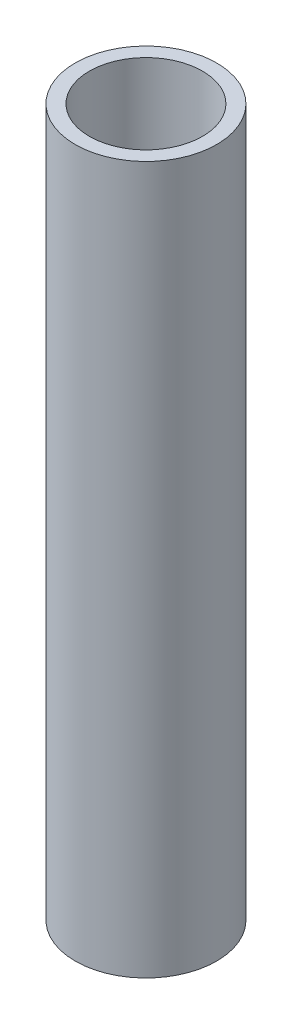
SolidWorks part; units mm, degrees
ref_plane "Front Plane" through (0, 0, 0) normal (0, 0, 1) x (1, 0, 0)
ref_plane "Top Plane" through (0, 0, 0) normal (0, 1, 0) x (1, 0, 0)
ref_plane "Right Plane" through (0, 0, 0) normal (1, 0, 0) x (0, 0, -1)
sketch "Sketch1" plane through (0, 0, 0) normal (0, 1, 0) x (1, 0, 0)
  circle A0 centre (0, 0) radius 10
  circle A1 centre (0, 0) radius 8
  dimension "D1" = 20
  dimension "D2" = 2
extrude "Boss-Extrude1" add sketch "Sketch1" along normal blind 100
